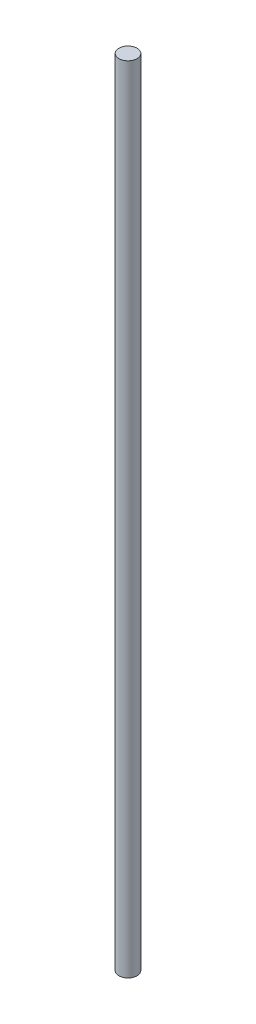
SolidWorks part; units mm, degrees
ref_plane "Front Plane" through (0, 0, 0) normal (0, 0, 1) x (1, 0, 0)
ref_plane "Top Plane" through (0, 0, 0) normal (0, 1, 0) x (1, 0, 0)
ref_plane "Right Plane" through (0, 0, 0) normal (1, 0, 0) x (0, 0, -1)
sketch "Sketch1" plane through (0, 0, 0) normal (0, 1, 0) x (1, 0, 0)
  circle A0 centre (0, 0) radius 4
  dimension "D1" = 8
extrude "Boss-Extrude1" add sketch "Sketch1" along normal blind 350.52
